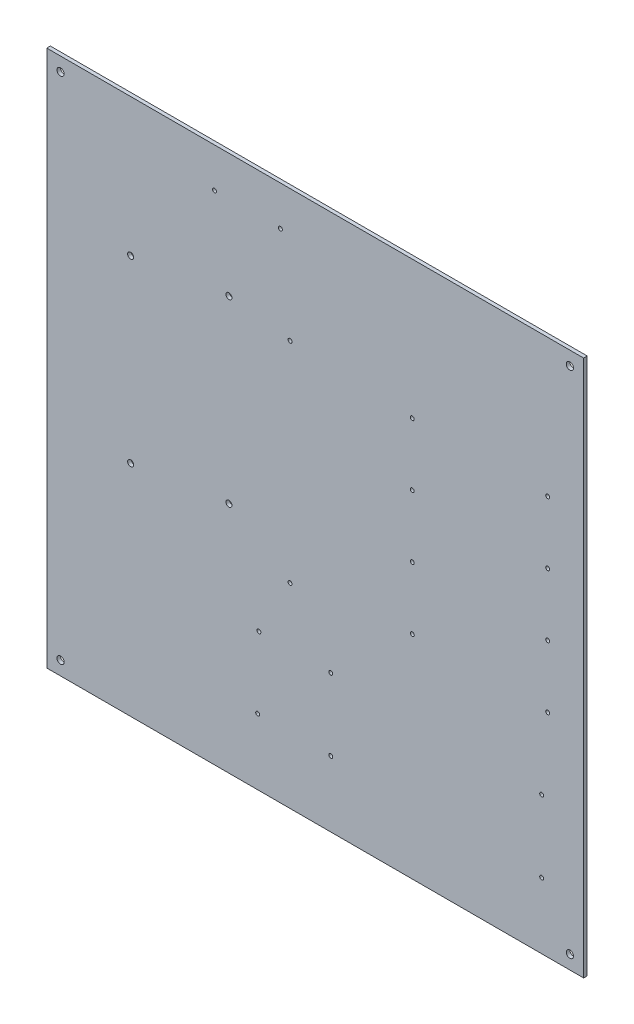
SolidWorks part; units mm, degrees
material "6061-T6 (SS)"
ref_plane "Piano frontale" through (0, 0, 0) normal (0, 0, 1) x (1, 0, 0)
ref_plane "Piano superiore" through (0, 0, 0) normal (0, 1, 0) x (1, 0, 0)
ref_plane "Piano destro" through (0, 0, 0) normal (1, 0, 0) x (0, 0, -1)
sketch "Schizzo1" plane through (0, 0, 0) normal (0, 0, 1) x (1, 0, 0)
  line L0 (0, 224) -> (448, 224) construction
  line L1 (0, 0) -> (448, 0)
  line L2 (0, 0) -> (0, 448)
  line L3 (0, 448) -> (448, 448)
  line L4 (448, 0) -> (448, 448)
  line L5 (224, 448) -> (224, 0) construction
  line L10 (0, 448) -> (0, 224) construction
  line L11 (0, 448) -> (0, 224) construction
  circle A0 centre (11.5, 436.5) radius 3
  circle A1 centre (436.5, 436.5) radius 3
  circle A2 centre (11.5, 11.5) radius 3
  circle A3 centre (436.5, 11.5) radius 3
  circle A4 centre (418, 177) radius 1.65
  circle A5 centre (305, 177) radius 1.65
  circle A6 centre (418, 229) radius 1.65
  circle A7 centre (305, 229) radius 1.65
  circle A8 centre (418, 281) radius 1.65
  circle A9 centre (305, 281) radius 1.65
  circle A10 centre (418, 333) radius 1.65
  circle A11 centre (305, 333) radius 1.65
  circle A12 centre (140, 415) radius 1.65
  circle A13 centre (195, 415) radius 1.65
  circle A14 centre (70, 333) radius 2.5
  circle A15 centre (70, 183) radius 2.5
  circle A16 centre (237, 55) radius 1.65
  circle A17 centre (237, 115) radius 1.65
  circle A18 centre (413, 115) radius 1.65
  circle A19 centre (413, 55) radius 1.65
  circle A20 centre (152, 344.7696) radius 2.5
  circle A21 centre (152, 194.7696) radius 2.5
  circle A22 centre (203, 338) radius 1.65
  circle A23 centre (203, 163) radius 1.65
  circle A24 centre (177, 115) radius 1.65
  circle A25 centre (176, 55) radius 1.65
  point P82 (253.9707, 256)
  point P89 (253.9707, 224)
  point P96 (253.9707, 192)
  point P103 (253.9707, 384)
  point P110 (253.9707, 352)
  point P117 (253.9707, 320)
  point P141 (253.9707, 288)
  point P148 (253.9707, 160)
  point P155 (253.9707, 128)
  point P162 (253.9707, 96)
  point P169 (253.9707, 64)
  point P179 (280.1758, 232.4048)
  point P193 (280.1085, 282.4047)
  point P207 (280.0413, 332.4047)
  dimension "D5" = 11.5
  dimension "D14" = 4
  dimension "D23" = 150
  dimension "D21" = 115
  dimension "D18" = 140
  dimension "D16" = 55
  dimension "D17" = 3.3
  dimension "D9" = 55
  dimension "D10" = 3.3
  dimension "D20" = 150
  dimension "D3" = 6
  dimension "D8" = 3.3
  dimension "D13" = 113
  dimension "D15" = 33
  dimension "D19" = 70
  dimension "D22" = 152
  dimension "D24" = 5
  dimension "D25" = 203
  dimension "D27" = 110
  dimension "D28" = 3.3
  dimension "D30" = 60
  dimension "D1" = 448
  dimension "D2" = 448
  dimension "D4" = 11.5
  dimension "D6" = 35
  dimension "D7" = 176
  dimension "D11" = 177
  dimension "D12" = 30
  dimension "D26" = 175
  dimension "D29" = 60
  dimension "D31" = 115
extrude "Estrusione-Estrusione1" add sketch "Schizzo1" against normal blind 3
